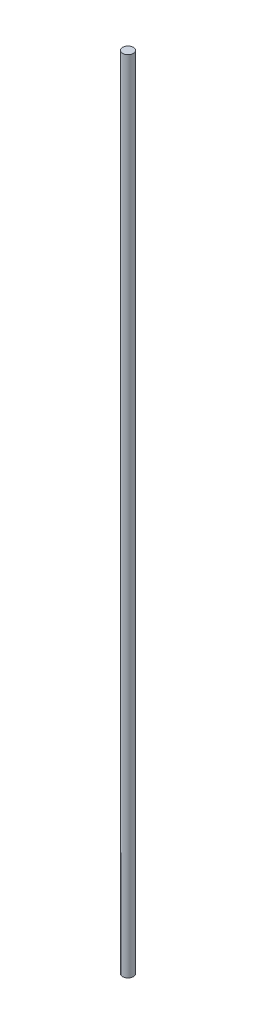
SolidWorks part; units mm, degrees
ref_plane "前视基准面" through (0, 0, 0) normal (0, 0, 1) x (1, 0, 0)
ref_plane "上视基准面" through (0, 0, 0) normal (0, 1, 0) x (1, 0, 0)
ref_plane "右视基准面" through (0, 0, 0) normal (1, 0, 0) x (0, 0, -1)
ref_plane "基准面4" through (0, 0, 0) normal (0, 0, -1) x (-1, 0, 0)
sketch "草图1" plane through (0, 0, 0) normal (0, 0, -1) x (-1, 0, 0)
  line L0 (-202, -300) -> (-200, -300)
  line L1 (-200, -300) -> (-200, 0)
  line L2 (-200, 0) -> (-202, 0)
  line L3 (-202, 0) -> (-202, -300)
  line L4 (-200, -300) -> (-200, 0) construction
revolve "旋转1" add sketch "草图1" angle 360 about L4
